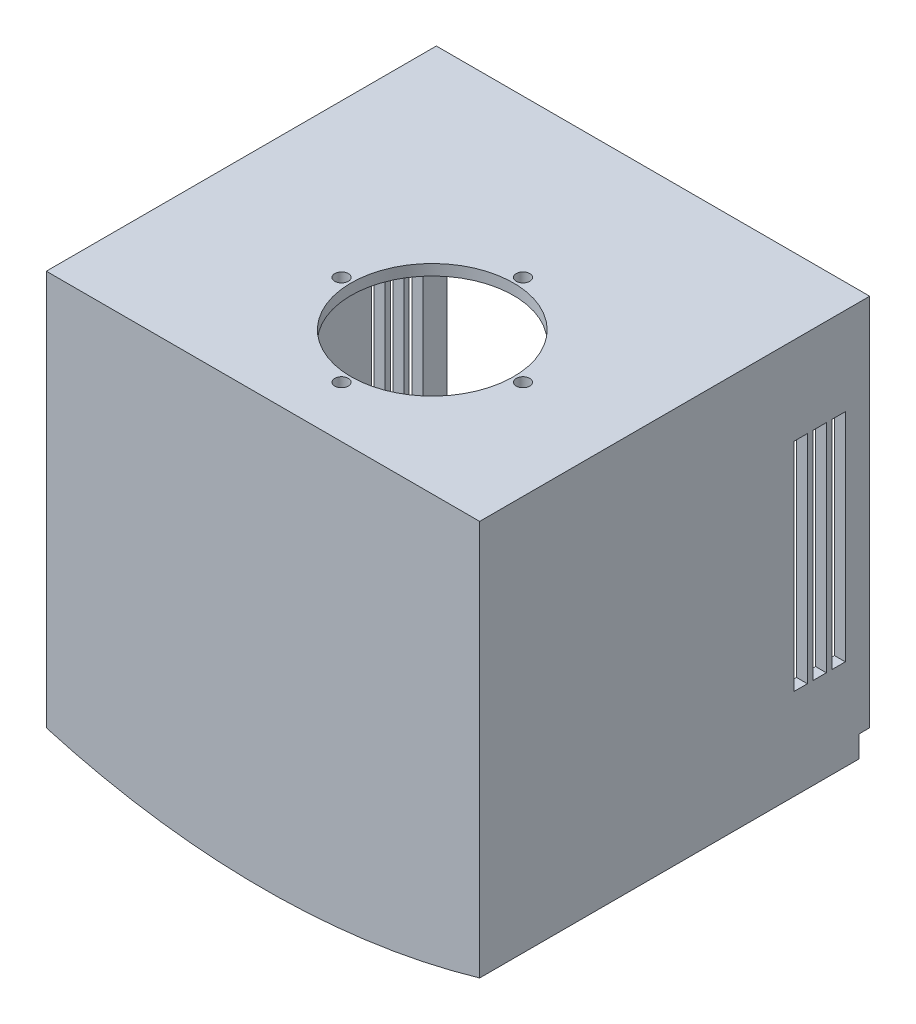
SolidWorks part; units mm, degrees
ref_plane "Front Plane" through (0, 0, 0) normal (0, 0, 1) x (1, 0, 0)
ref_plane "Top Plane" through (0, 0, 0) normal (0, 1, 0) x (1, 0, 0)
ref_plane "Right Plane" through (0, 0, 0) normal (1, 0, 0) x (0, 0, -1)
sketch "Sketch1" plane through (0, 0, 0) normal (0, 0, 1) x (1, 0, 0)
  line L0 (-40, -137.2917) -> (-40, -64.2917)
  line L1 (-40, -64.2917) -> (40, -64.2917)
  line L2 (40, -64.2917) -> (40, -137.2917)
  arc A0 (-40, -137.2917) -> (40, -137.2917) centre (0, 0) ccw
  dimension "D1" = 143
  dimension "D2" = 80
  dimension "D3" = 73
extrude "Boss-Extrude1" add sketch "Sketch1" along normal mid plane 70
shell "Shell1" thickness 2
sketch "Sketch3" plane through (0, -64.2917, 0) normal (0, 1, 0) x (1, 0, 0)
  line L2 (-22.3931, -8.75) -> (31.0689, -8.75) construction
  line L3 (5, 15.7489) -> (5, -27.0035) construction
  circle A0 centre (5, -8.75) radius 15
  circle A1 centre (5, 8) radius 1.25
  circle A2 centre (21.75, -8.75) radius 1.25
  circle A3 centre (-11.75, -8.75) radius 1.25
  circle A4 centre (5, -25.5) radius 1.25
  dimension "D3" = 30
  dimension "D6" = 2.5
  dimension "D7" = 2.5
  dimension "D4" = 16.75
  dimension "D5" = 16.75
extrude "Cut-Extrude2" cut sketch "Sketch3" against normal blind 2
sketch "Sketch4" plane through (40, 0, 0) normal (1, 0, 0) x (0, 0, -1)
  line L0 (-35, -64.2917) -> (35, -64.2917) construction
  line L1 (25.5, -120.4967) -> (23, -120.4967)
  line L2 (25.5, -120.4967) -> (25.5, -80.4967)
  line L3 (25.5, -80.4967) -> (23, -80.4967)
  line L4 (23, -120.4967) -> (23, -80.4967)
  line L5 (25.5, -120.4967) -> (23, -80.4967) construction
  line L6 (25.5, -80.4967) -> (23, -120.4967) construction
  line L8 (35, -137.2917) -> (35, -64.2917) construction
  line L9 (29, -120.4967) -> (26.5, -120.4967)
  line L10 (29, -120.4967) -> (29, -80.4967)
  line L11 (29, -80.4967) -> (26.5, -80.4967)
  line L12 (26.5, -120.4967) -> (26.5, -80.4967)
  line L13 (29, -120.4967) -> (26.5, -80.4967) construction
  line L14 (29, -80.4967) -> (26.5, -120.4967) construction
  line L15 (30, -120.4967) -> (32.5, -120.4967)
  line L16 (30, -120.4967) -> (30, -80.4967)
  line L17 (30, -80.4967) -> (32.5, -80.4967)
  line L18 (32.5, -120.4967) -> (32.5, -80.4967)
  line L19 (30, -120.4967) -> (32.5, -80.4967) construction
  line L20 (30, -80.4967) -> (32.5, -120.4967) construction
  point P0 (24.25, -100.4967)
  point P9 (27.75, -100.4967)
  point P14 (31.25, -100.4967)
  dimension "D1" = 40
  dimension "D2" = 3.75
  dimension "D3" = 2.5
  dimension "D4" = 36.205
  dimension "D5" = 2.5
  dimension "D6" = 3.5
  dimension "D7" = 2.5
  dimension "D8" = 3.5
extrude "Cut-Extrude3" cut sketch "Sketch4" against normal through all both and the other way through all
sketch "Sketch6" plane through (0, 0, -35) normal (0, 0, -1) x (-1, 0, 0)
  line L0 (-40, -64.2917) -> (-40, -133.2917)
  line L1 (40, -64.2917) -> (-40, -64.2917)
  line L2 (40, -133.2917) -> (40, -64.2917)
  line L3 (-40, -137.2917) -> (-40, -64.2917) construction
  line L4 (-40, -64.2917) -> (40, -64.2917) construction
  line L6 (38, -66.2917) -> (-38, -66.2917)
  line L8 (-38, -66.2917) -> (-38, -131.7829) construction
  line L9 (38, -131.7829) -> (38, -66.2917) construction
  line L10 (-38, -66.2917) -> (-38, -133.2917)
  line L11 (-38, -135.7829) -> (-38, -66.2917) construction
  line L12 (38, -66.2917) -> (38, -133.2917)
  line L13 (38, -66.2917) -> (38, -135.7829) construction
  line L14 (-40, -133.2917) -> (-38, -133.2917)
  line L15 (38, -133.2917) -> (40, -133.2917)
  arc A2 (-40, -133.2917) -> (40, -133.2917) centre (0, 4) ccw construction
  arc A3 (-38, -131.7829) -> (38, -131.7829) centre (0, 4) ccw construction
  dimension "D1" = 69
  dimension "D3" = 76
  dimension "D2" = 80
  dimension "D4" = 67
extrude "Boss-Extrude2" add sketch "Sketch6" along normal blind 2
